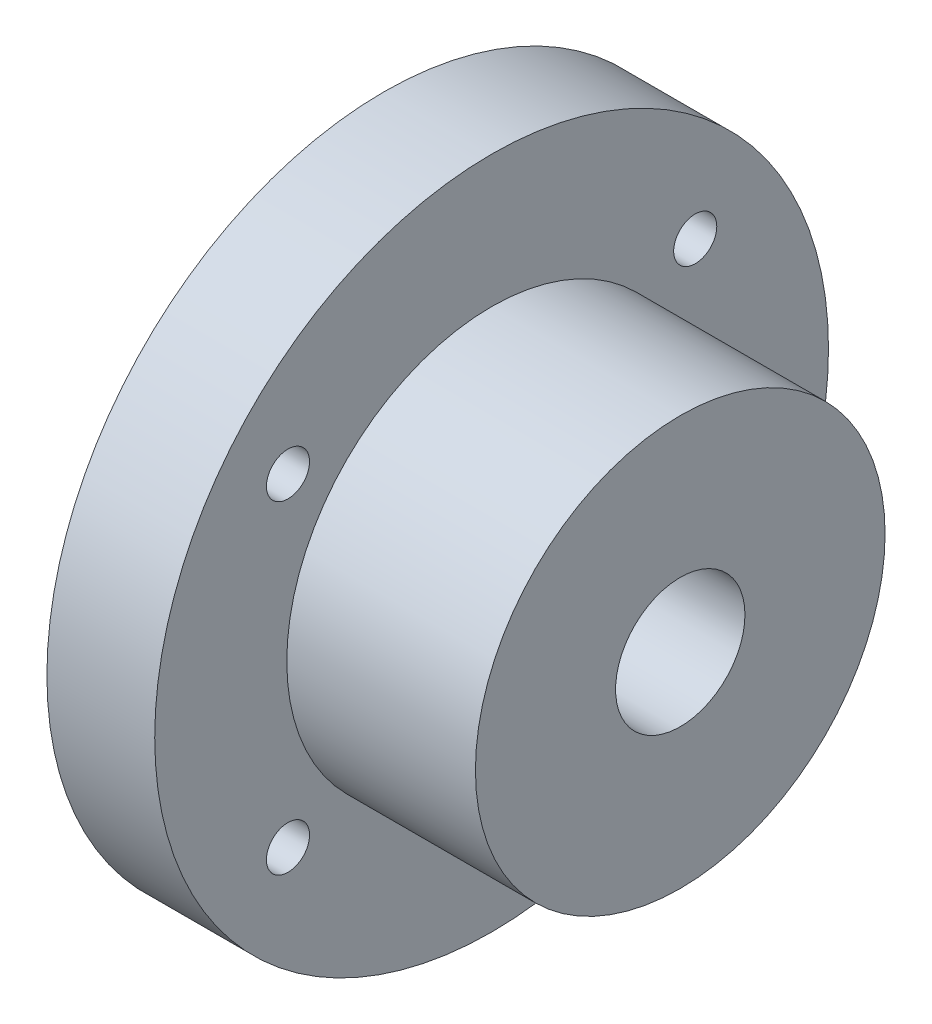
SolidWorks part; units mm, degrees
material "AISI 1020"
ref_plane "Plano frontal" through (0, 0, 0) normal (0, 0, 1) x (1, 0, 0)
ref_plane "Plano superior" through (0, 0, 0) normal (0, 1, 0) x (1, 0, 0)
ref_plane "Plano direito" through (0, 0, 0) normal (1, 0, 0) x (0, 0, -1)
sketch "Esboço1" plane through (0, 0, 0) normal (1, 0, 0) x (0, 0, -1)
  line L20 (-37.775, -30) -> (37.775, 30) construction
  line L21 (37.775, -30) -> (-37.775, 30) construction
  circle A24 centre (0, 0) radius 62.5
  circle A25 centre (37.775, 30) radius 4
  circle A26 centre (-37.775, 30) radius 4
  circle A27 centre (37.775, -30) radius 4
  circle A28 centre (-37.775, -30) radius 4
  point P0 (0, 0)
  dimension "D3" = 125
  dimension "D1" = 60
  dimension "D2" = 75.55
extrude "Ressalto-extrusão1" add sketch "Esboço1" along normal blind 20
sketch "Esboço2" plane through (20, 0, 0) normal (1, 0, 0) x (0, 0, -1)
  circle A0 centre (0, 0) radius 38
extrude "Ressalto-extrusão2" add sketch "Esboço2" along normal blind 35
sketch "Esboço4" plane through (55, 0, 0) normal (1, 0, 0) x (0, 0, -1)
  circle A0 centre (0, 0) radius 12
  dimension "D1" = 24
extrude "Corte-extrusão1" cut sketch "Esboço4" against normal blind 25
cosmetic thread "Representação de rosca2" parameters "D2"=24
cosmetic thread "Representação de rosca3" parameters "D2"=27
thread "Rosca1" pitch 2 start angle 0, offset 0, length 0, pitch 2, diameter 20
ref_plane "Plano1" through (55, 0, 10) normal (0, -1, 0) x (0, 0, 1)
sketch "Perfil da rosca1" plane through (55, 0, 10) normal (0, -1, 0) x (0, 0, 1)
  line L0 (0, 0) -> (0, 2) construction
  line L11 (0, 0) -> (0, 1.75)
  line L12 (0, 1.75) -> (-1.0825, 1.125)
  line L13 (-1.0825, 1.125) -> (-1.0825, 0.625)
  line L15 (-1.0825, 0.625) -> (0, 0)
  line L17 (-1.0825, 0.875) -> (0, 0.875) construction
  point P2 (0, 0)
  dimension "Pitch" = 2
  dimension "Profile_Angle" = 60
  dimension "Profile_Land" = 0.5
  dimension "Profile_Height" = 1.0825
